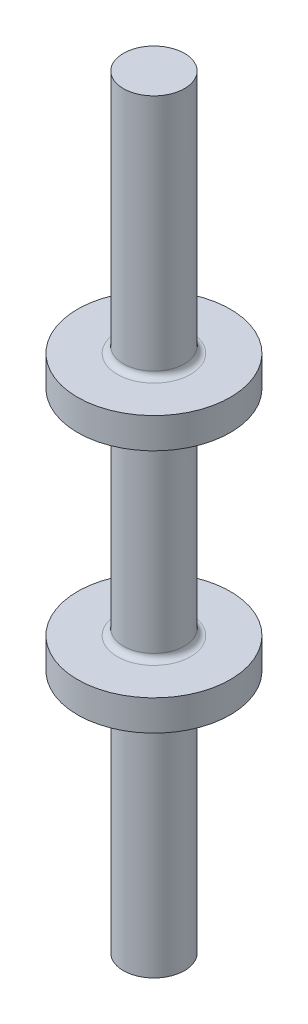
SolidWorks part; units mm, degrees
ref_plane "Front Plane" through (0, 0, 0) normal (0, 0, 1) x (1, 0, 0)
ref_plane "Top Plane" through (0, 0, 0) normal (0, 1, 0) x (1, 0, 0)
ref_plane "Right Plane" through (0, 0, 0) normal (1, 0, 0) x (0, 0, -1)
sketch "Sketch1" plane through (0, 0, 0) normal (0, 0, 1) x (1, 0, 0)
  line L0 (0, 0) -> (1, 0)
  line L1 (1, 0) -> (1, 8)
  line L2 (1, 8) -> (2.5, 8)
  line L3 (2.5, 8) -> (2.5, 9)
  line L4 (2.5, 9) -> (1, 9)
  line L5 (1, 9) -> (1, 16)
  line L6 (1, 16) -> (2.5, 16)
  line L7 (2.5, 16) -> (2.5, 17)
  line L8 (2.5, 17) -> (1, 17)
  line L9 (1, 17) -> (1, 25)
  line L10 (1, 25) -> (0, 25)
  line L11 (0, 25) -> (0, 0)
  point P12 (1, 12.5)
  point P14 (0, 12.5)
  dimension "D1" = 25
  dimension "D2" = 1
  dimension "D3" = 1.5
  dimension "D4" = 1
  dimension "D5" = 8
revolve "Revolve1" add sketch "Sketch1" angle 360 about L11
fillet "Fillet1" radius 0.2 4 edges at (0, 8, 1) (0, 9, 1) (0, 16, 1) (0, 17, 1)
